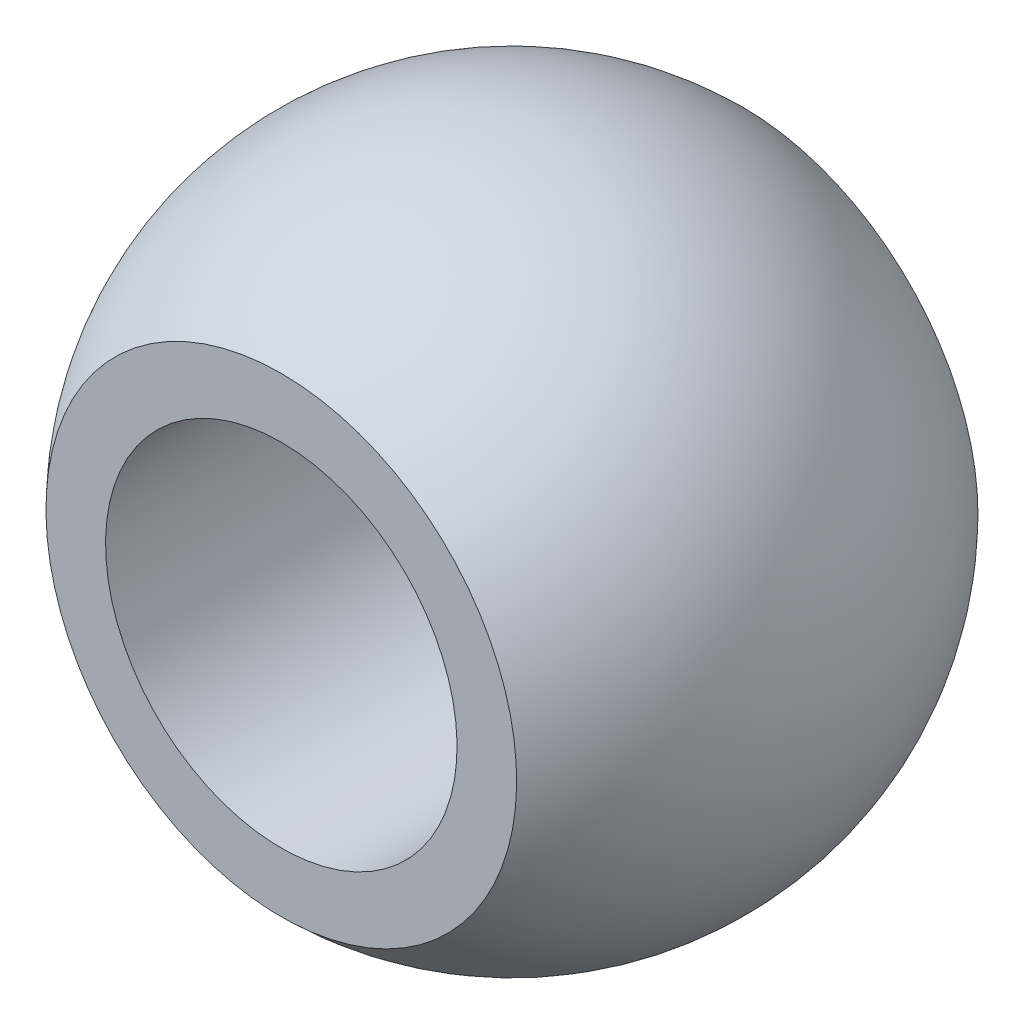
SolidWorks part; units mm, degrees
material "Acero aleado"
ref_plane "Alzado" through (0, 0, 0) normal (0, 0, 1) x (1, 0, 0)
ref_plane "Planta" through (0, 0, 0) normal (0, 1, 0) x (1, 0, 0)
ref_plane "Vista lateral" through (0, 0, 0) normal (1, 0, 0) x (0, 0, -1)
sketch "Croquis1" plane through (0, 0, 0) normal (0, 0, 1) x (1, 0, 0)
  line L0 (0, 15) -> (0, -15)
  arc A0 (0, 15) -> (0, -15) centre (0, 0) ccw
  dimension "EsferaE" = 30
revolve "Revolución1" add sketch "Croquis1" angle 360 about L0
sketch "Croquis2" plane through (0, 0, 0) normal (0, 0, 1) x (1, 0, 0)
  circle A0 centre (0, 0) radius 8
  dimension "B" = 16
extrude "Cortar-Extruir1" cut sketch "Croquis2" against normal through all both and the other way through all
sketch "Croquis3" plane through (0, 0, 0) normal (1, 0, 0) x (0, 0, -1)
  line L0 (-10.5, 0) -> (10.5, 0) construction
  line L1 (-10.5, -10.7121) -> (-10.5, 10.7121)
  line L2 (-20.5, -10.7121) -> (-20.5, 10.7121)
  line L3 (-10.5, 10.7121) -> (-20.5, 10.7121)
  line L4 (-10.5, -10.7121) -> (-20.5, -10.7121)
  line L5 (0, -1000) -> (0, 49000) construction
  line L6 (10.5, -10.7121) -> (10.5, 10.7121)
  line L7 (10.5, 10.7121) -> (20.5, 10.7121)
  line L8 (20.5, -10.7121) -> (20.5, 10.7121)
  line L9 (10.5, -10.7121) -> (20.5, -10.7121)
  arc A0 (12.6886, 8) -> (-12.6886, 8) centre (0, 0) ccw construction
  point P4 (0, 0)
  point P11 (-10.5, 0)
  dimension "D1" = 10
  dimension "W" = 21
extrude "Cortar-Extruir2" cut sketch "Croquis3" against normal through all both and the other way through all
